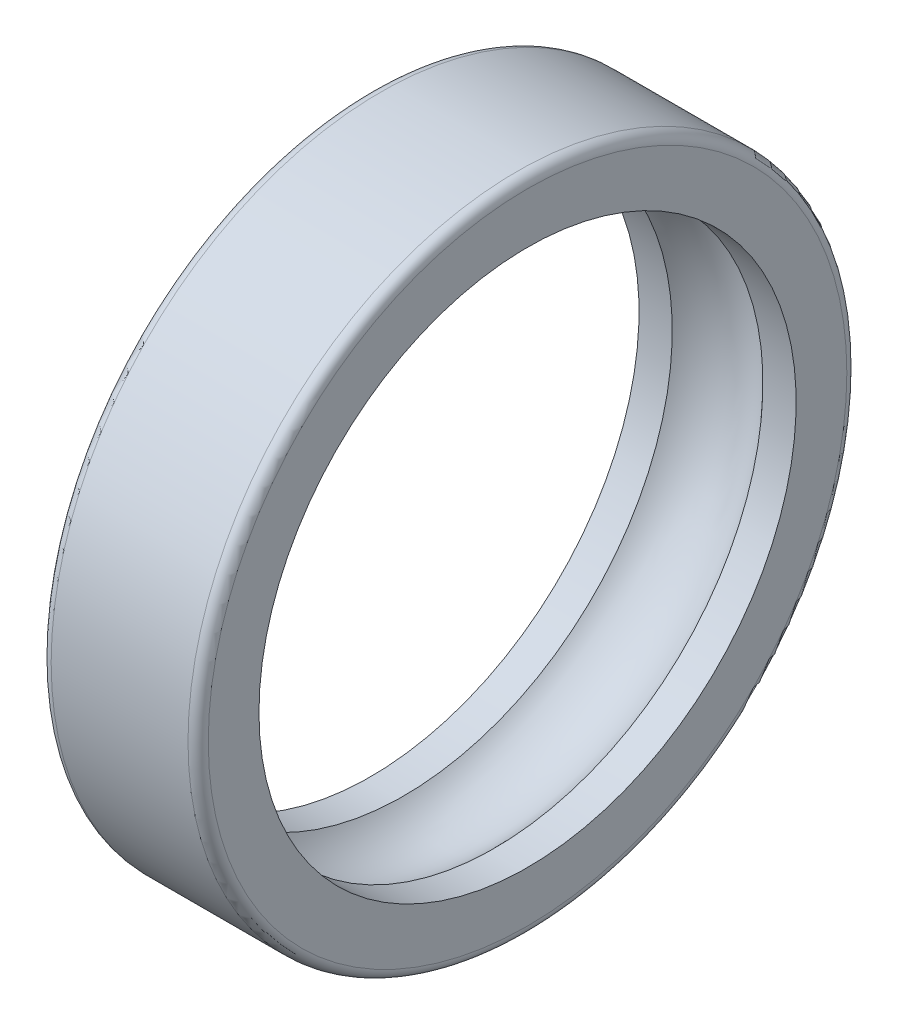
SolidWorks part; units mm, degrees
ref_plane "Front Plane" through (0, 0, 0) normal (0, 0, 1) x (1, 0, 0)
ref_plane "Top Plane" through (0, 0, 0) normal (0, 1, 0) x (1, 0, 0)
ref_plane "Right Plane" through (0, 0, 0) normal (1, 0, 0) x (0, 0, -1)
sketch "Sketch1" plane through (0, 0, 0) normal (0, 0, 1) x (1, 0, 0)
  line L0 (-15.5, 0) -> (39.2494, 0) construction
  line L1 (0, 0) -> (0, 59) construction
  line L2 (15.5, 65) -> (-15.5, 65)
  line L3 (15.5, 65) -> (15.5, 53)
  line L4 (15.5, 53) -> (8.9443, 53)
  line L5 (-15.5, 65) -> (-15.5, 53)
  line L6 (15.5, 65) -> (-15.5, 53) construction
  line L7 (15.5, 53) -> (-15.5, 65) construction
  line L8 (-8.9443, 53) -> (-15.5, 53)
  arc A0 (-8.9443, 53) -> (8.9443, 53) centre (0, 45) cw
  point P0 (0, 59)
  dimension "D5" = 12
  dimension "D1" = 31
  dimension "D2" = 53
  dimension "D3" = 65
  dimension "D4" = 8
revolve "Revolve1" add sketch "Sketch1" angle 360 about L0
fillet "Fillet1" radius 2 2 edges at (15.5, 0, 65) (-15.5, 0, 65)
